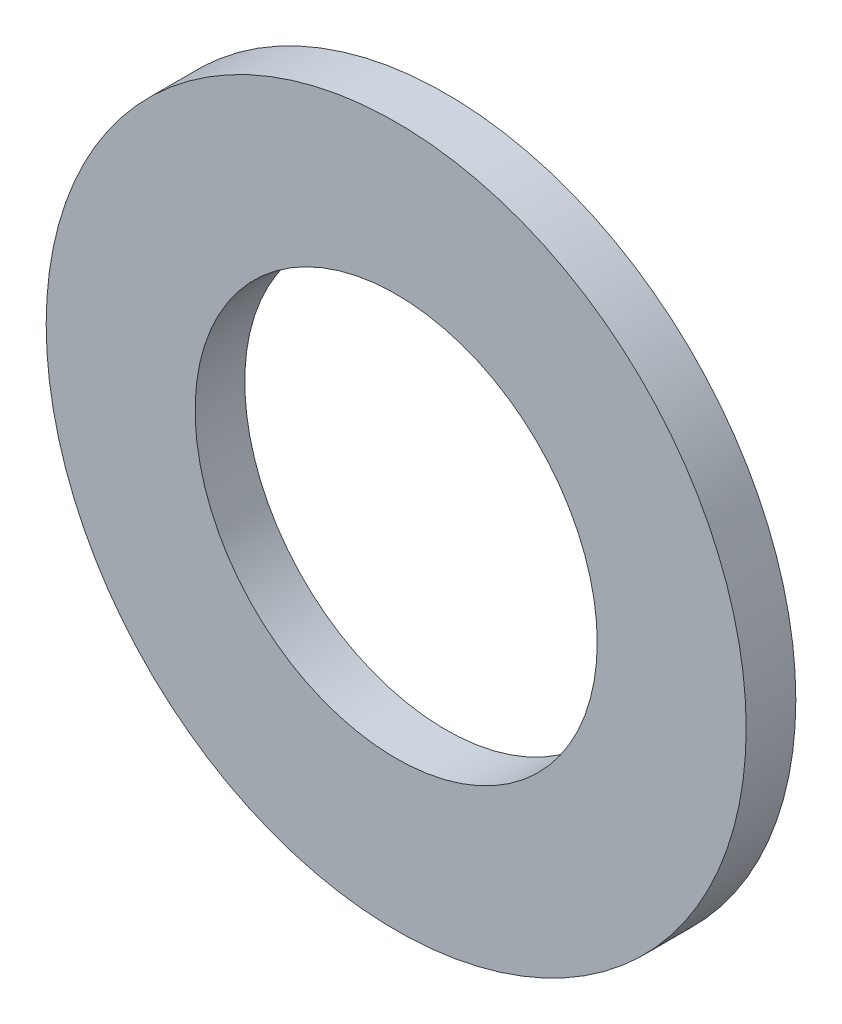
SolidWorks part; units mm, degrees
ref_plane "Front Plane" through (0, 0, 0) normal (0, 0, 1) x (1, 0, 0)
ref_plane "Top Plane" through (0, 0, 0) normal (0, 1, 0) x (1, 0, 0)
ref_plane "Right Plane" through (0, 0, 0) normal (1, 0, 0) x (0, 0, -1)
sketch "Sketch1" plane through (0, 0, 0) normal (0, 0, 1) x (1, 0, 0)
  circle A0 centre (0, 0) radius 4.05
  circle A1 centre (0, 0) radius 7.05
  dimension "D1" = 8.1
  dimension "D2" = 3
extrude "Boss-Extrude1" add sketch "Sketch1" along normal blind 1
